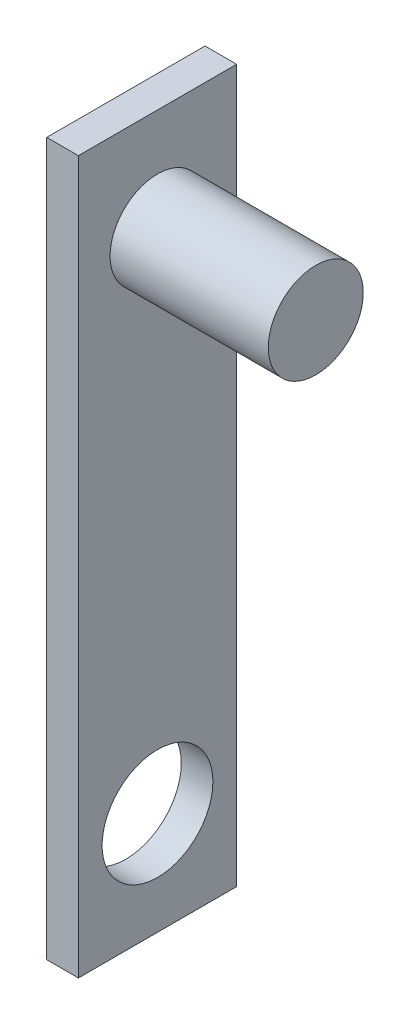
SolidWorks part; units mm, degrees
ref_plane "Front Plane" through (0, 0, 0) normal (0, 0, 1) x (1, 0, 0)
ref_plane "Top Plane" through (0, 0, 0) normal (0, 1, 0) x (1, 0, 0)
ref_plane "Right Plane" through (0, 0, 0) normal (1, 0, 0) x (0, 0, -1)
sketch "Sketch1" plane through (0, 0, 0) normal (1, 0, 0) x (0, 0, -1)
  line L1 (-5, -22.5) -> (5, -22.5)
  line L2 (-5, -22.5) -> (-5, 22.5)
  line L3 (-5, 22.5) -> (5, 22.5)
  line L4 (5, -22.5) -> (5, 22.5)
  line L5 (-5, -22.5) -> (5, 22.5) construction
  line L6 (-5, 22.5) -> (5, -22.5) construction
  point P0 (0, 0)
  dimension "D1" = 45
  dimension "D2" = 10
extrude "Boss-Extrude1" add sketch "Sketch1" along normal blind 2
sketch "Sketch2" plane through (2, 0, 0) normal (1, 0, 0) x (0, 0, -1)
  circle A0 centre (0, -16) radius 3.5
  dimension "D2" = 7
  dimension "D1" = 16
extrude "Cut-Extrude1" cut sketch "Sketch2" against normal up to surface (2 mm away) up to face at (0, 0, 0)
sketch "Sketch3" plane through (2, 0, 0) normal (1, 0, 0) x (0, 0, -1)
  circle A0 centre (0, 16) radius 3
  dimension "D1" = 16
extrude "Boss-Extrude2" add sketch "Sketch3" along normal blind 10
